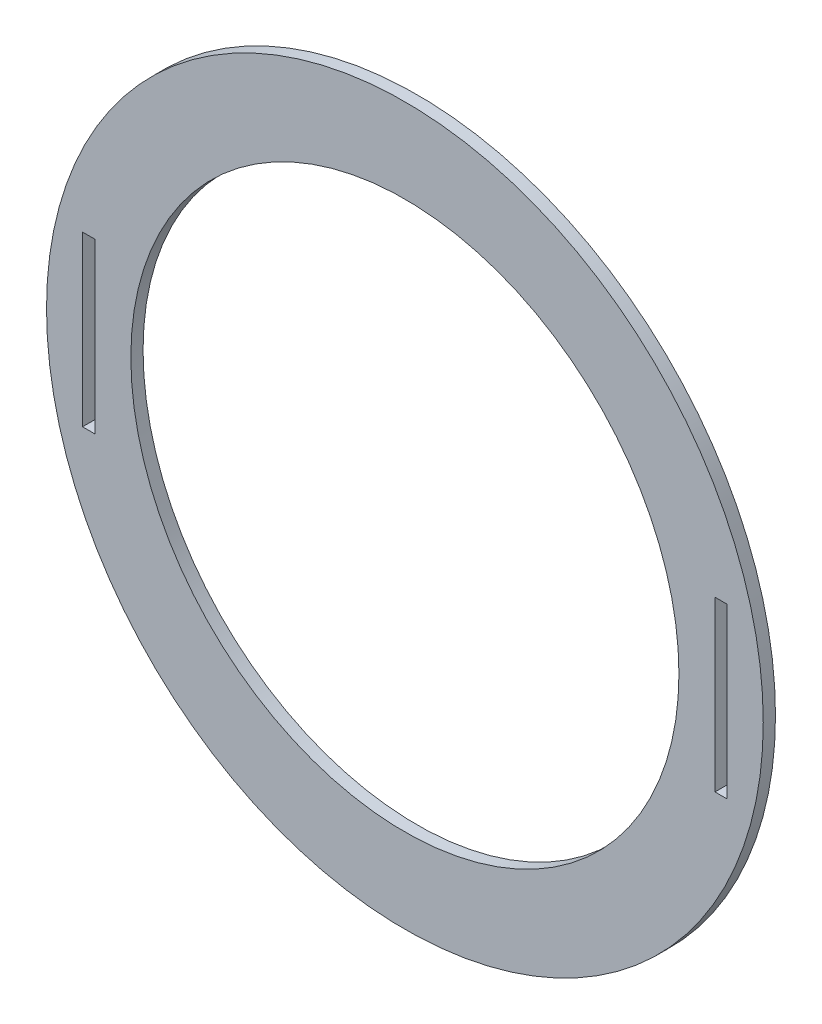
SolidWorks part; units mm, degrees
ref_plane "Front Plane" through (0, 0, 0) normal (0, 0, 1) x (1, 0, 0)
ref_plane "Top Plane" through (0, 0, 0) normal (0, 1, 0) x (1, 0, 0)
ref_plane "Right Plane" through (0, 0, 0) normal (1, 0, 0) x (0, 0, -1)
sketch "Sketch1" plane through (0, 0, 0) normal (0, 0, 1) x (1, 0, 0)
  line L0 (-65, 0) -> (-85, 0) construction
  line L1 (-76.45, 20) -> (-73.55, 20)
  line L2 (-76.45, 20) -> (-76.45, -20)
  line L3 (-76.45, -20) -> (-73.55, -20)
  line L4 (-73.55, 20) -> (-73.55, -20)
  line L5 (-76.45, 20) -> (-73.55, -20) construction
  line L6 (-76.45, -20) -> (-73.55, 20) construction
  line L7 (0, 0) -> (0, 23.7761) construction
  line L8 (76.45, -20) -> (73.55, 20) construction
  line L9 (76.45, 20) -> (73.55, -20) construction
  line L10 (65, 0) -> (85, 0) construction
  line L11 (73.55, 20) -> (73.55, -20)
  line L12 (76.45, -20) -> (73.55, -20)
  line L13 (76.45, 20) -> (76.45, -20)
  line L14 (76.45, 20) -> (73.55, 20)
  circle A0 centre (0, 0) radius 65
  circle A1 centre (0, 0) radius 85
  point P4 (-75, 0)
  point P19 (75, 0)
  dimension "D1" = 130
  dimension "D2" = 170
  dimension "D3" = 40
  dimension "D4" = 2.9
extrude "Boss-Extrude1" add sketch "Sketch1" along normal blind 2.9
